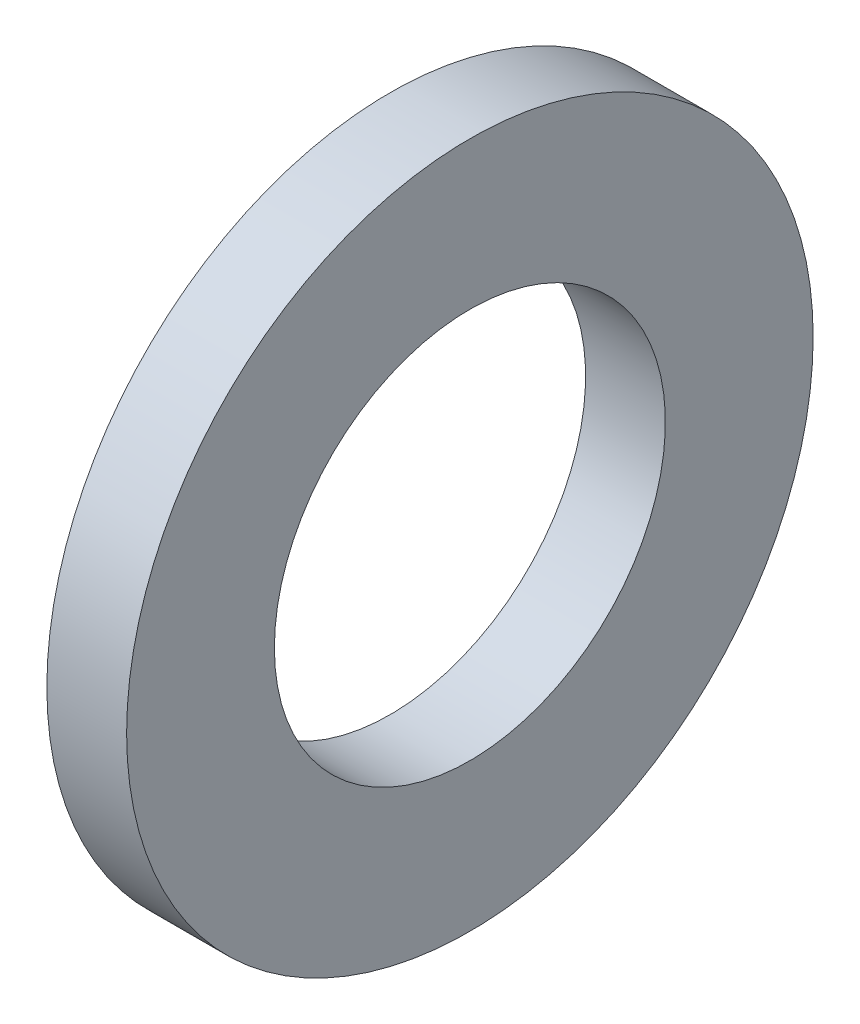
SolidWorks part; units mm, degrees
ref_plane "Front Plane" through (0, 0, 0) normal (0, 0, 1) x (1, 0, 0)
ref_plane "Top Plane" through (0, 0, 0) normal (0, 1, 0) x (1, 0, 0)
ref_plane "Right Plane" through (0, 0, 0) normal (1, 0, 0) x (0, 0, -1)
sketch "Sketch2" plane through (0, 0, 0) normal (0, 0, 1) x (1, 0, 0)
  line L0 (0, 0) -> (58.591, 0) construction
  line L2 (0, 0) -> (18.4, 0)
  line L3 (0, 0) -> (0, 2.5)
  line L4 (0, 2.5) -> (18.4, 2.5)
  line L5 (18.4, 0) -> (18.4, 2.5)
  line L6 (6.0094, 2.5) -> (6.0094, 6)
  line L11 (6.0094, 6) -> (9.9794, 6)
  line L16 (12.9794, 6) -> (12.9794, 3)
  line L17 (12.9794, 3) -> (13.6398, 3)
  line L18 (13.6398, 3) -> (13.6398, 2.5)
  line L19 (13.6398, 2.5) -> (6.0094, 2.5)
  line L22 (13.6398, 2.5) -> (16.1198, 2.5)
  line L23 (13.6398, 2.5) -> (13.6398, 4)
  line L24 (13.6398, 4) -> (16.1198, 4)
  line L25 (16.1198, 2.5) -> (16.1198, 4)
  line L27 (6.0094, 6) -> (9.9794, 6)
  line L28 (6.0094, 6) -> (6.0094, 9)
  line L29 (6.0094, 9) -> (9.9794, 9)
  line L30 (9.9794, 6) -> (9.9794, 9)
  line L31 (6.0094, 9) -> (6.0094, 8.25)
  line L32 (6.0094, 8.25) -> (5.0094, 8.25)
  line L33 (8.6609, 22.001) -> (8.6609, 12.476) construction
  line L34 (5.0094, 12.476) -> (12.3124, 12.476)
  line L35 (9.9794, 9) -> (12.3124, 9)
  line L36 (5.0094, 7.9375) -> (1.7709, 7.9375)
  line L37 (5.0094, 8.25) -> (5.0094, 12.476)
  line L38 (5.0094, 7.9375) -> (5.0094, 13.9365)
  line L39 (5.0094, 13.9365) -> (1.7709, 13.9365)
  line L40 (1.7709, 7.9375) -> (1.7709, 13.9365)
  line L41 (5.0094, 22.001) -> (12.3124, 22.001)
  line L42 (5.0094, 22.001) -> (5.0094, 30.1625)
  line L43 (5.0094, 30.1625) -> (12.3124, 30.1625)
  line L44 (12.3124, 22.001) -> (12.3124, 30.1625)
  line L49 (16.6398, 22.001) -> (16.6398, 7.5)
  line L51 (23.0198, 7.5) -> (23.0198, 6.5)
  line L54 (16.1198, 4) -> (13.6398, 4)
  line L56 (18.0398, 7.5) -> (23.0198, 7.5)
  line L57 (13.3124, 22.001) -> (16.6398, 22.001)
  line L58 (16.1198, 3.5) -> (20.0198, 3.5)
  line L59 (29.9098, 14) -> (26.9098, 11)
  line L60 (4.0094, 31.75) -> (18.0398, 31.75)
  line L61 (18.0398, 7.5) -> (23.0198, 7.5)
  line L62 (18.0398, 7.5) -> (18.0398, 12)
  line L63 (18.0398, 12) -> (23.0198, 12)
  line L64 (23.0198, 7.5) -> (23.0198, 12)
  line L65 (18.0398, 31.75) -> (18.0398, 12)
  line L66 (23.0198, 11) -> (26.9098, 11)
  line L67 (34.8098, 23) -> (31.3098, 19.5)
  line L68 (35.8098, 31) -> (38.7998, 33.99)
  line L69 (29.9098, 14) -> (29.9098, 15)
  line L70 (29.9098, 15) -> (22.9398, 15)
  line L71 (22.9398, 15) -> (21.0398, 15)
  line L72 (18.0398, 7.5) -> (16.6398, 7.5)
  line L73 (21.0398, 15) -> (21.0398, 43)
  line L74 (19.6115, 40) -> (9.6516, 40)
  line L75 (9.6516, 40) -> (4.0094, 40)
  line L76 (21.0398, 43) -> (19.6115, 43)
  line L77 (22.9398, 15) -> (29.9098, 15)
  line L78 (22.9398, 15) -> (22.9398, 21)
  line L79 (22.9398, 21) -> (29.9098, 21)
  line L80 (29.9098, 15) -> (29.9098, 21)
  line L81 (9.6516, 40) -> (19.6115, 40)
  line L82 (9.6516, 40) -> (9.6516, 50)
  line L83 (9.6516, 50) -> (19.6115, 50)
  line L84 (19.6115, 40) -> (19.6115, 50)
  line L85 (4.0094, 40) -> (4.0094, 31.75)
  line L86 (12.9794, 3) -> (12.9794, 2.5)
  line L87 (31.3098, 19.5) -> (29.9098, 19.5)
  line L88 (21.4694, 63.5) -> (21.4694, 51.308)
  line L89 (21.4694, 63.5) -> (25.9398, 63.5)
  line L90 (25.9398, 63.5) -> (25.9398, 25)
  line L91 (27.8398, 25) -> (25.9398, 25)
  line L92 (9.6516, 48) -> (8.2233, 48)
  line L93 (8.2233, 48) -> (8.2233, 53.476)
  line L94 (8.2233, 53.476) -> (19.6115, 53.476)
  line L95 (19.6115, 53.476) -> (19.6115, 50)
  line L96 (13.9174, 63.001) -> (13.9174, 53.476) construction
  line L97 (8.2233, 63.001) -> (19.6115, 63.001)
  line L98 (8.2233, 63.001) -> (8.2233, 68.2625)
  line L99 (8.2233, 68.2625) -> (19.6115, 68.2625)
  line L100 (19.6115, 63.001) -> (19.6115, 68.2625)
  line L101 (12.9794, 6) -> (11.9794, 6)
  line L102 (8.2233, 44.825) -> (4.9848, 44.825)
  line L103 (8.2233, 44.825) -> (8.2233, 54.9365)
  line L104 (8.2233, 54.9365) -> (4.9848, 54.9365)
  line L106 (9.9794, 6) -> (10.8794, 6)
  line L107 (27.8398, 25) -> (34.8098, 25)
  line L108 (34.8098, 25) -> (34.8098, 23)
  line L109 (0, 0) -> (-2, 0)
  line L110 (0, 0) -> (0, 11)
  line L111 (27.8398, 25) -> (34.8098, 25)
  line L112 (27.8398, 25) -> (27.8398, 32.5)
  line L113 (27.8398, 32.5) -> (34.8098, 32.5)
  line L114 (34.8098, 25) -> (34.8098, 32.5)
  line L115 (35.8098, 31) -> (34.8098, 31)
  line L116 (27.8398, 32.5) -> (27.8398, 64.5)
  line L117 (20.5849, 74.025) -> (6.2499, 74.025)
  line L118 (6.2499, 74.025) -> (6.2499, 76.2)
  line L119 (38.7998, 47.29) -> (30.8398, 55.25)
  line L120 (0, 11) -> (-2, 11)
  line L121 (38.7998, 43.815) -> (30.8623, 43.815)
  line L123 (-4.8152, 69.85) -> (1.5348, 76.2)
  line L124 (38.7998, 47.29) -> (38.7998, 33.99)
  line L125 (-2, 0) -> (-2, 11)
  line L126 (38.7998, 37.465) -> (30.8623, 37.465)
  line L127 (30.8623, 43.815) -> (30.8623, 37.465)
  line L128 (6.0094, 2.5) -> (6.0094, 0)
  line L129 (-0.0152, 63.5) -> (-0.0152, 30)
  line L132 (4.9848, 63.5) -> (-0.0152, 63.5)
  line L136 (-1.8152, 30) -> (-11.7752, 30)
  line L138 (-13.7752, 25.4) -> (-2, 25.4)
  line L139 (-2, 25.4) -> (-2, 11.5)
  line L140 (27.8398, 64.5) -> (20.5849, 64.5)
  line L141 (-1.8152, 30) -> (-11.7752, 30)
  line L142 (-1.8152, 30) -> (-1.8152, 39)
  line L143 (-1.8152, 39) -> (-11.7752, 39)
  line L144 (-11.7752, 30) -> (-11.7752, 39)
  line L145 (20.5849, 64.5) -> (20.5849, 74.025)
  line L146 (-12.7752, 37) -> (-12.7752, 47.29)
  line L147 (-12.7752, 37) -> (-11.7752, 37)
  line L148 (30.8398, 55.25) -> (30.8398, 76.2)
  line L149 (11.9794, 6) -> (11.9794, 5.45)
  line L154 (-2, 11.5) -> (0.5, 11.5)
  line L155 (4.9848, 60.6197) -> (24.0348, 60.6197)
  line L160 (4.9848, 60.6197) -> (4.9848, 55.8572)
  line L161 (4.9848, 55.8572) -> (24.0348, 55.8572)
  line L166 (24.0348, 60.6197) -> (24.0348, 55.8572)
  line L167 (4.9848, 60.6197) -> (24.0348, 55.8572) construction
  line L172 (4.9848, 55.8572) -> (24.0348, 60.6197) construction
  line L173 (24.0348, 62.2072) -> (25.9398, 62.2072)
  line L174 (11.9794, 5.45) -> (10.8794, 5.45)
  line L175 (10.8794, 6) -> (10.8794, 5.45)
  line L176 (24.0348, 62.2072) -> (24.0348, 54.2697)
  line L177 (24.0348, 54.2697) -> (25.9398, 54.2697)
  line L178 (25.9398, 62.2072) -> (25.9398, 54.2697)
  line L179 (24.0348, 62.2072) -> (25.9398, 54.2697) construction
  line L180 (24.0348, 54.2697) -> (25.9398, 62.2072) construction
  line L181 (3, 19.6197) -> (15.7, 19.6197)
  line L182 (3, 19.6197) -> (3, 14.8572)
  line L183 (3, 14.8572) -> (15.7, 14.8572)
  line L184 (15.7, 19.6197) -> (15.7, 14.8572)
  line L185 (3, 19.6197) -> (15.7, 14.8572) construction
  line L186 (3, 14.8572) -> (15.7, 19.6197) construction
  line L187 (15.7, 21.2072) -> (16.6398, 21.2072)
  line L188 (15.7, 21.2072) -> (15.7, 13.2697)
  line L189 (15.7, 13.2697) -> (16.6398, 13.2697)
  line L190 (16.6398, 21.2072) -> (16.6398, 13.2697)
  line L191 (15.7, 21.2072) -> (16.6398, 13.2697) construction
  line L192 (15.7, 13.2697) -> (16.6398, 21.2072) construction
  line L193 (0.5, 11.5) -> (0.5, 6.9375)
  line L194 (0.5, 6.9375) -> (1.7709, 6.9375)
  line L195 (23.0198, 6.5) -> (20.0198, 3.5)
  line L196 (4.9848, 63.5) -> (4.9848, 54.9365)
  line L197 (3, 43.825) -> (4.9848, 43.825)
  line L198 (1.7709, 6.9375) -> (1.7709, 7.9375)
  line L199 (6.0094, 0) -> (12.9794, 0)
  line L200 (12.9794, 0) -> (12.9794, 2.5)
  line L201 (18.0398, 31.75) -> (18.0398, 35.875)
  line L202 (18.0398, 35.875) -> (21.0398, 35.875)
  line L203 (30.8398, 76.2) -> (6.2499, 76.2)
  line L204 (2.8049, 69.85) -> (7.2499, 69.85) construction
  line L205 (7.2499, 67.4688) -> (26.2999, 67.4688)
  line L206 (7.2499, 74.025) -> (7.2499, 64.5)
  line L207 (7.2499, 64.5) -> (-1.8152, 64.5)
  line L208 (-1.8152, 64.5) -> (-1.8152, 39)
  line L209 (-12.7752, 47.29) -> (-4.8152, 55.25)
  line L210 (-4.8152, 55.25) -> (-4.8152, 69.85)
  line L211 (7.2499, 67.4688) -> (7.2499, 72.2312)
  line L212 (7.2499, 72.2312) -> (26.2999, 72.2313)
  line L213 (26.2999, 67.4688) -> (26.2999, 72.2313)
  line L214 (26.2999, 73.8187) -> (30.8398, 73.8187)
  line L215 (26.2999, 73.8187) -> (26.2999, 65.8813)
  line L216 (26.2999, 65.8813) -> (30.8398, 65.8813)
  line L217 (30.8398, 73.8187) -> (30.8398, 65.8813)
  line L218 (2.8049, 72.2313) -> (25.0299, 72.2313)
  line L219 (2.8049, 72.2313) -> (2.8049, 67.4687)
  line L220 (2.8049, 67.4687) -> (25.0299, 67.4687)
  line L221 (25.0299, 72.2313) -> (25.0299, 67.4687)
  line L222 (25.0299, 69.85) -> (20.5849, 69.85) construction
  line L223 (21.4694, 51.308) -> (22.9398, 51.308)
  line L224 (22.9398, 51.308) -> (22.9398, 21)
  line L225 (13.6398, 4) -> (13.6398, 12.2697)
  line L226 (13.6398, 12.2697) -> (13.3124, 12.2697)
  line L227 (13.3124, 12.2697) -> (13.3124, 22.001)
  line L228 (12.3124, 9) -> (12.3124, 12.476)
  line L229 (-1.8152, 30) -> (-0.0152, 30)
  line L230 (8.2233, 65.6317) -> (2.8049, 65.6317) construction
  line L231 (19.6115, 65.6317) -> (25.0299, 65.6317) construction
  line L232 (1.5348, 76.2) -> (6.2499, 76.2)
  line L233 (-11.7752, 30) -> (-13.7752, 30)
  line L234 (-13.7752, 30) -> (-13.7752, 25.4)
  line L235 (3, 13.9365) -> (3, 43.825)
  line L236 (4.9848, 54.9365) -> (4.9848, 44.825)
  line L237 (4.9848, 43.825) -> (4.9848, 44.825)
  circle A0 centre (26.8898, 25.95) radius 0.95
  circle A1 centre (21.9898, 15.95) radius 0.95
  circle A2 centre (17.3398, 8.2) radius 0.7
  circle A3 centre (10.4294, 6.45) radius 0.45
  circle A4 centre (-0.9152, 30.9) radius 0.9
  point P7 (24.9873, 58.2385)
  point P131 (16.1699, 17.2385)
  point P135 (14.5098, 58.2385)
  point P146 (9.35, 17.2385)
sketch "Sketch3" plane through (0, 0, 0) normal (0, 0, 1) x (1, 0, 0)
  line L0 (5.0094, 7.9375) -> (5.0094, 13.9365) construction
  line L1 (5.0094, 13.9365) -> (1.7709, 13.9365) construction
  line L2 (1.7709, 7.9375) -> (1.7709, 13.9365) construction
  line L3 (5.0094, 7.9375) -> (1.7709, 7.9375) construction
  line L4 (5.0094, 7.9375) -> (5.0094, 13.9365)
  line L5 (5.0094, 13.9365) -> (1.7709, 13.9365)
  line L6 (1.7709, 7.9375) -> (1.7709, 13.9365)
  line L7 (5.0094, 7.9375) -> (1.7709, 7.9375)
revolve "Revolve1" add sketch "Sketch3" angle 360 about L0
